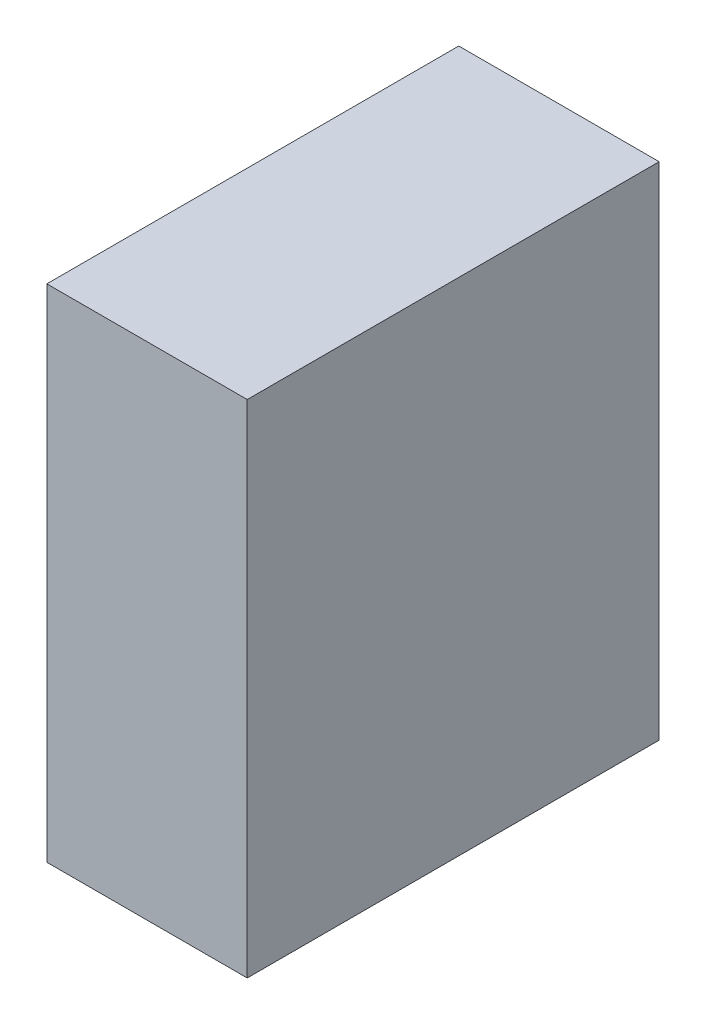
SolidWorks part; units mm, degrees
ref_plane "Front Plane" through (0, 0, 0) normal (0, 0, 1) x (1, 0, 0)
ref_plane "Top Plane" through (0, 0, 0) normal (0, 1, 0) x (1, 0, 0)
ref_plane "Right Plane" through (0, 0, 0) normal (1, 0, 0) x (0, 0, -1)
sketch "Sketch2" plane through (0, 0, 0) normal (0, 1, 0) x (1, 0, 0)
  line L1 (-90, -185) -> (90, -185)
  line L2 (-90, -185) -> (-90, 185)
  line L3 (-90, 185) -> (90, 185)
  line L4 (90, -185) -> (90, 185)
  line L5 (-90, -185) -> (90, 185) construction
  line L6 (-90, 185) -> (90, -185) construction
  point P0 (0, 0)
  dimension "D1" = 180
  dimension "D2" = 370
extrude "Boss-Extrude1" add sketch "Sketch2" along normal blind 450
